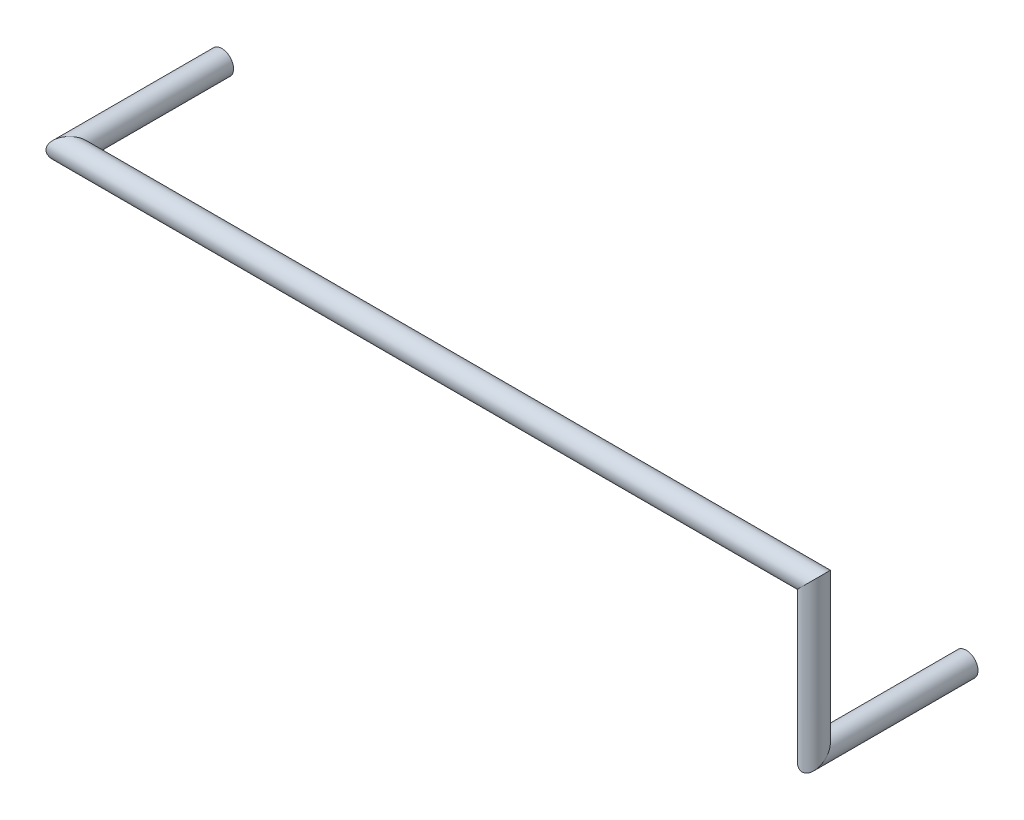
SolidWorks part; units mm, degrees
ref_plane "Front Plane" through (0, 0, 0) normal (0, 0, 1) x (1, 0, 0)
ref_plane "Top Plane" through (0, 0, 0) normal (0, 1, 0) x (1, 0, 0)
ref_plane "Right Plane" through (0, 0, 0) normal (1, 0, 0) x (0, 0, -1)
sketch3d "3DSketch3"
  line L0 (0, 0, 0) -> (0, 0, 2.6)
  line L1 (0, 0, 2.6) -> (0, 2.54, 2.6)
  line L2 (0, 2.54, 2.6) -> (-12.7, 2.54, 2.6)
  line L3 (-12.7, 2.54, 2.6) -> (-12.7, 2.54, 0)
  point P6 (53.1457, 2.54, 2.6)
  point P7 (-7.9868, 2.54, 2.6)
  dimension "D2" = 2.6
  dimension "D1" = 2.6
  dimension "D3" = 2.54
  dimension "D4" = 12.7
sweep "Sweep1" add path "3DSketch3" circular profile diameter 0.4 parameters "D3"=0.4
equation "\"D2@3DSketch3\"=\"D1@3DSketch3\""
equation "\"D4@3DSketch3\"=2.54*5"
